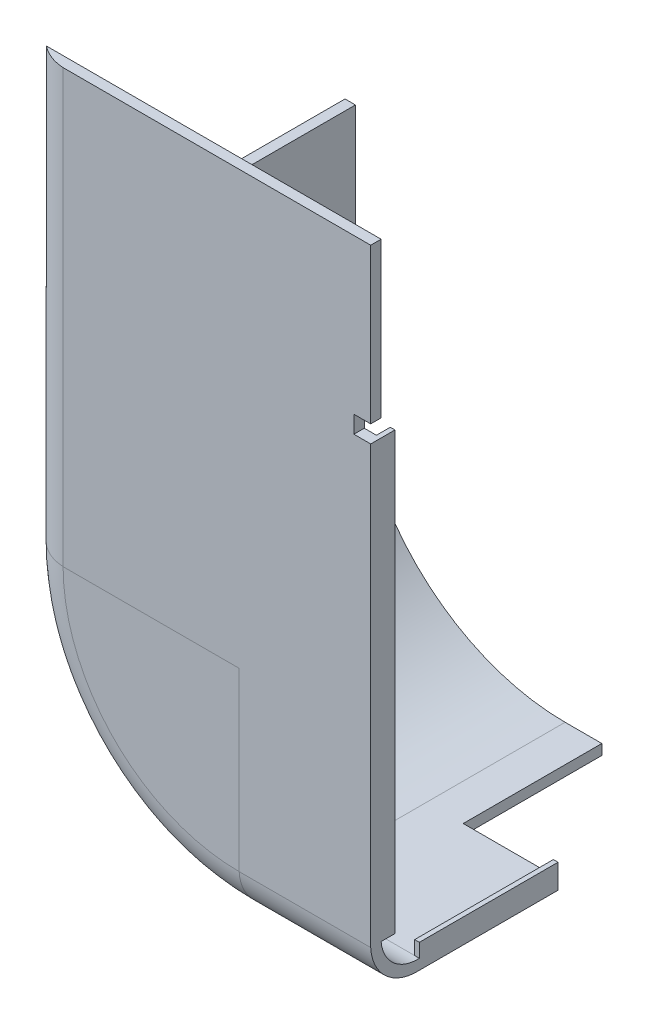
SolidWorks part; units mm, degrees
material "ABS"
ref_plane "Front Plane" through (0, 0, 0) normal (0, 0, 1) x (1, 0, 0)
ref_plane "Top Plane" through (0, 0, 0) normal (0, 1, 0) x (1, 0, 0)
ref_plane "Right Plane" through (0, 0, 0) normal (1, 0, 0) x (0, 0, -1)
sketch "Sketch1" plane through (0, 0, 0) normal (0, 0, 1) x (1, 0, 0)
  line L0 (-98.6, 98.6) -> (-98.6, -38.1)
  line L1 (-101.6, 101.6) -> (-101.6, -38.1)
  line L2 (-101.6, 101.6) -> (101.6, 101.6)
  line L3 (101.6, 101.6) -> (101.6, -38.1)
  line L4 (-38.1, -101.6) -> (38.1, -101.6)
  line L5 (-98.6, 98.6) -> (98.6, 98.6)
  line L6 (98.6, 98.6) -> (98.6, -38.1)
  line L7 (-38.1, -98.6) -> (38.1, -98.6)
  arc A0 (38.1, -101.6) -> (101.6, -38.1) centre (38.1, -38.1) ccw
  arc A1 (-101.6, -38.1) -> (-38.1, -101.6) centre (-38.1, -38.1) ccw
  arc A4 (98.6, -38.1) -> (38.1, -98.6) centre (38.1, -38.1) cw
  arc A5 (-38.1, -98.6) -> (-98.6, -38.1) centre (-38.1, -38.1) cw
  dimension "D5" = 63.5
  dimension "D6" = 63.5
  dimension "D1" = 203.2
  dimension "D2" = 139.7
  dimension "D3" = 139.7
  dimension "D4" = 76.2
  dimension "D7" = 101.6
  dimension "D8" = 101.6
  dimension "D9" = 3
  dimension "D10" = 3
  dimension "D11" = 3
  dimension "D12" = 3
  dimension "D13" = 0
  dimension "D14" = 0
  dimension "D15" = 0
  dimension "D16" = 0
extrude "Boss-Extrude1" add sketch "Sketch1" along normal blind 60 contours L1 A1 L4 A0 L3 L2 | L0 A5 L7 A4 L6 L5
sketch "Sketch3" plane through (0, 101.6, 0) normal (0, 1, 0) x (1, 0, 0)
  line L1 (-101.6, -60) -> (101.6, -60) construction
  line L2 (-38.1, -91.0391) -> (-88.9, -91.0391)
  line L3 (-98.6, -60) -> (-98.6, -80)
  line L4 (-38.1, -94.0391) -> (-38.1, -91.0391)
  line L7 (-98.6, -60) -> (-101.6, -60)
  line L9 (-101.6, -60) -> (-101.6, -80)
  line L10 (-38.1, -94.0391) -> (-88.9, -94.0391)
  arc A0 (-98.6, -80) -> (-88.9, -91.0391) centre (-88.0412, -80.5032) ccw
  arc A4 (-101.6, -80) -> (-88.9, -94.0391) centre (-88.2305, -80.6695) ccw
  dimension "D1" = 63.5
  dimension "D2" = 3
  dimension "D3" = 3
  dimension "D5" = 20
sketch "Sketch5" plane through (0, 0, 60) normal (0, 0, 1) x (1, 0, 0)
  line L0 (-100.1, 101.6) -> (-100.1, -38.1)
  line L1 (-98.6, 101.6) -> (-101.6, 101.6) construction
  line L2 (-101.6, 101.6) -> (-101.6, -38.1) construction
  line L3 (-38.1, -98.6) -> (-38.1, -101.6) construction
  line L4 (38.1, -98.6) -> (38.1, -101.6) construction
  line L5 (98.6, -38.1) -> (101.6, -38.1) construction
  line L6 (38.1, -100.1) -> (-38.1, -100.1)
  line L7 (100.1, -38.1) -> (100.1, 101.6)
  line L8 (-101.6, 101.6) -> (101.6, 101.6) construction
  arc A0 (-100.1, -38.1) -> (-38.1, -100.1) centre (-38.1, -38.1) ccw
  arc A1 (38.1, -100.1) -> (100.1, -38.1) centre (38.1, -38.1) ccw
  dimension "D1" = 0
  dimension "D2" = 1.5
  dimension "D3" = 0
sweep "Sweep2" add profiles "Sketch3" path "Sketch5"
sketch "Sketch6" plane through (0, 0, 94.0391) normal (0, 0, 1) x (1, 0, 0)
  line L0 (38.1, -38.1) -> (-38.1, -38.1)
  line L1 (-38.1, -38.1) -> (-38.1, 101.6)
  line L2 (-38.1, 101.6) -> (38.1, 101.6)
  line L3 (38.1, 101.6) -> (38.1, -38.1)
extrude "Boss-Extrude3" add sketch "Sketch6" against normal blind 3
sketch "Sketch7" plane through (0, 101.6, 0) normal (0, 1, 0) x (1, 0, 0)
  line L1 (122.4585, 44.29) -> (-132.2369, 44.29)
  line L2 (122.4585, 44.29) -> (122.4585, -91.0391)
  line L3 (122.4585, -91.0391) -> (-132.2369, -91.0391)
  line L4 (-132.2369, 44.29) -> (-132.2369, -91.0391)
  line L5 (122.4585, 44.29) -> (-132.2369, -91.0391) construction
  line L6 (122.4585, -91.0391) -> (-132.2369, 44.29) construction
  point P0 (-4.8892, -23.3746)
extrude "Cut-Extrude1" cut sketch "Sketch7" against normal blind 76.2
sketch "Sketch8" plane through (0, 0, 94.0391) normal (0, 0, 1) x (1, 0, 0)
  line L0 (0, 0) -> (0, 39.4405) construction
  line L2 (-5, 41.9405) -> (5, 41.9405)
  line L3 (-5, 41.9405) -> (-5, 36.9405)
  line L4 (-5, 36.9405) -> (5, 36.9405)
  line L5 (5, 41.9405) -> (5, 36.9405)
  line L6 (-5, 41.9405) -> (5, 36.9405) construction
  line L7 (-5, 36.9405) -> (5, 41.9405) construction
extrude "Cut-Extrude2" cut sketch "Sketch8" against normal through all
sketch "Sketch9" plane through (0, -101.6, 0) normal (0, -1, 0) x (-1, 0, 0)
  line L0 (38.1, 0) -> (-38.1, 0) construction
  line L1 (27.5, 0) -> (-27.5, 0)
  line L2 (27.5, 0) -> (27.5, -40)
  line L3 (27.5, -40) -> (-27.5, -40)
  line L4 (-27.5, 0) -> (-27.5, -40)
  line L5 (27.5, 0) -> (-27.5, -40) construction
  line L6 (27.5, -40) -> (-27.5, 0) construction
  line L7 (0, -20) -> (0, 0) construction
  point P0 (0, -20)
  dimension "D1" = 0
  dimension "D2" = 40
  dimension "D3" = 55
extrude "Cut-Extrude3" cut sketch "Sketch9" against normal through all
sketch "Sketch10" plane through (0, 101.6, 0) normal (0, 1, 0) x (1, 0, 0)
  line L0 (-88.9, -94.0391) -> (88.9, -94.0391) construction
  line L1 (100.3822, -101.2333) -> (-100.3822, -101.2333)
  line L2 (100.3822, -101.2333) -> (100.3822, -86.8449)
  line L3 (100.3822, -86.8449) -> (-100.3822, -86.8449)
  line L4 (-100.3822, -101.2333) -> (-100.3822, -86.8449)
  line L5 (100.3822, -101.2333) -> (-100.3822, -86.8449) construction
  line L6 (100.3822, -86.8449) -> (-100.3822, -101.2333) construction
  point P0 (0, -94.0391)
extrude "Cut-Extrude4" cut sketch "Sketch10" against normal blind 15
sketch "Sketch11" plane through (0, -98.6, 0) normal (0, 1, 0) x (1, 0, 0)
  line L0 (0, -40) -> (0, -80) construction
  line L1 (-27.5, -40) -> (27.5, -40) construction
  line L2 (-38.1, -80) -> (38.1, -80) construction
  line L3 (0, -80) -> (1.5, -80)
  line L4 (1.5, -80) -> (1.5, -40)
  line L5 (1.5, -40) -> (0, -40)
  line L6 (0, -80) -> (-1.5, -80)
  line L7 (-1.5, -80) -> (-1.5, -40)
  line L8 (-1.5, -40) -> (0, -40)
  dimension "D1" = 1.5
  dimension "D2" = 1.5
extrude "Boss-Extrude4" add sketch "Sketch11" along normal blind 4
sketch "Sketch12" plane through (0, 0, 91.0391) normal (0, 0, -1) x (-1, 0, 0)
  line L0 (0, -88.9) -> (0, 36.9405) construction
  line L1 (38.1, -88.9) -> (-38.1, -88.9) construction
  line L5 (-1.5, -88.9) -> (0, -88.9)
  line L6 (0, -88.9) -> (1.5, -88.9)
  line L7 (1.5, -88.9) -> (1.5, 36.9405)
  line L11 (-1.5, 36.9405) -> (1.5, 36.9405)
  line L12 (5, 36.9405) -> (-5, 36.9405) construction
  line L13 (-1.5, 36.9405) -> (-1.5, -88.9)
extrude "Boss-Extrude5" add sketch "Sketch12" along normal blind 4 contours L7 L11 L13 L5 L6
sketch "Sketch13" plane through (101.6, 0, 0) normal (1, 0, 0) x (0, 0, -1)
  line L1 (51.2296, -185.9364) -> (-130.3605, -185.9364)
  line L2 (51.2296, -185.9364) -> (51.2296, 169.0559)
  line L3 (51.2296, 169.0559) -> (-130.3605, 169.0559)
  line L4 (-130.3605, -185.9364) -> (-130.3605, 169.0559)
  line L5 (51.2296, -185.9364) -> (-130.3605, 169.0559) construction
  line L6 (51.2296, 169.0559) -> (-130.3605, -185.9364) construction
  point P0 (-39.5655, -8.4403)
extrude "Cut-Extrude5" cut sketch "Sketch13" against normal blind 101.75
